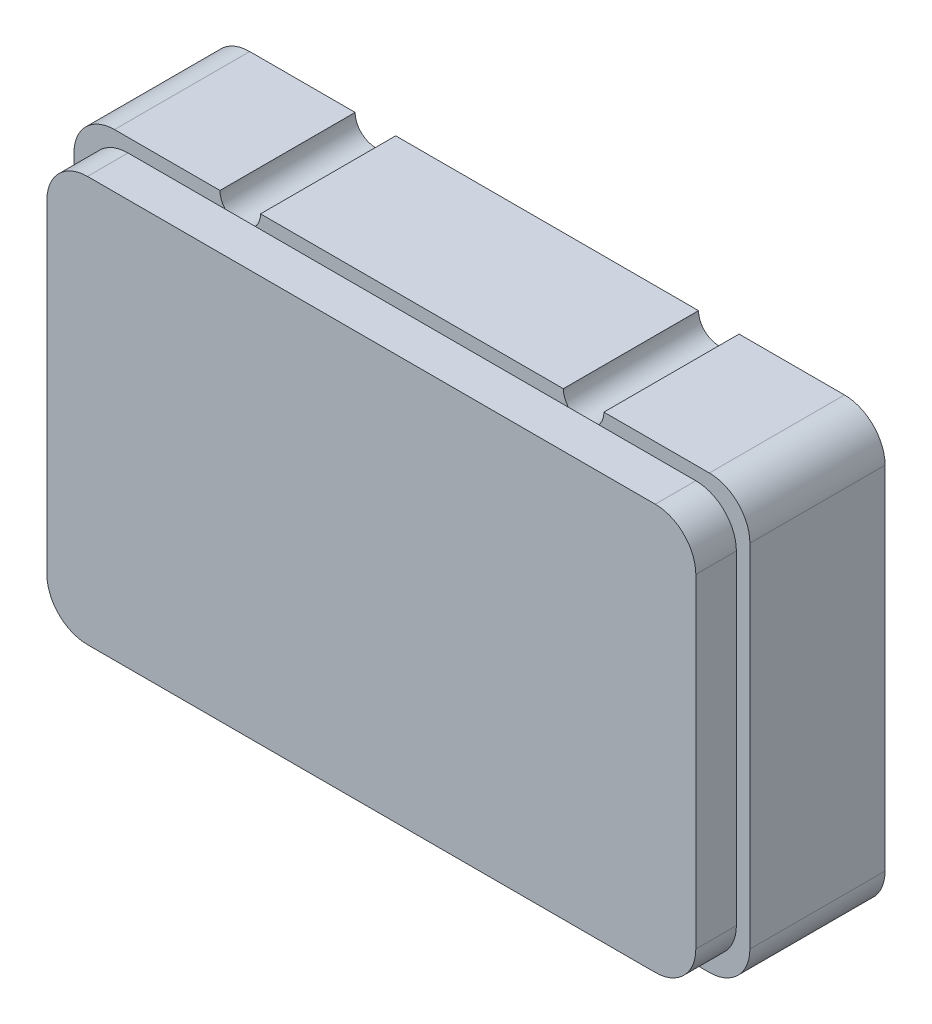
SolidWorks part; units mm, degrees
ref_plane "Front Plane" through (0, 0, 0) normal (0, 0, 1) x (1, 0, 0)
ref_plane "Top Plane" through (0, 0, 0) normal (0, 1, 0) x (1, 0, 0)
ref_plane "Right Plane" through (0, 0, 0) normal (1, 0, 0) x (0, 0, -1)
sketch "Sketch1" plane through (0, 0, 0) normal (0, 0, 1) x (1, 0, 0)
  line L1 (0, 0) -> (5, 0)
  line L2 (0, 0) -> (0, 3.2)
  line L3 (0, 3.2) -> (5, 3.2)
  line L4 (5, 0) -> (5, 3.2)
  dimension "D1" = 5
  dimension "D2" = 3.2
extrude "Boss-Extrude1" add sketch "Sketch1" along normal blind 1
sketch "Sketch2" plane through (0, 0, 1) normal (0, 0, 1) x (1, 0, 0)
  line L0 (2.5, 3.2) -> (2.5, 0) construction
  line L1 (0.1, 0.1) -> (4.9, 0.1)
  line L2 (0.1, 0.1) -> (0.1, 3.1)
  line L3 (0.1, 3.1) -> (4.9, 3.1)
  line L4 (4.9, 0.1) -> (4.9, 3.1)
  line L5 (5, 3.2) -> (0, 3.2) construction
  line L6 (0, 0) -> (5, 0) construction
  line L8 (0, 3.2) -> (0, 0) construction
  line L9 (0, 1.6) -> (5, 1.6) construction
  line L10 (5, 0) -> (5, 3.2) construction
  point P10 (2.5, 3.1)
  point P17 (0.1, 1.6)
  dimension "D1" = 4.8
  dimension "D2" = 3
extrude "Boss-Extrude2" add sketch "Sketch2" along normal blind 0.3
fillet "Fillet1" radius 0.3 4 edges at (4.9, 3.1, 1.15) (0.1, 3.1, 1.15) (0.1, 0.1, 1.15) (4.9, 0.1, 1.15)
fillet "Fillet2" radius 0.3 4 edges at (0, 3.2, 0.5) (0, 0, 0.5) (5, 0, 0.5) (5, 3.2, 0.5)
sketch "Sketch3" plane through (0, 0, 0) normal (0, 0, -1) x (-1, 0, 0)
  line L0 (-4.7, 3.2) -> (-0.3, 3.2) construction
  line L1 (-3.92, 3.2) -> (-3.62, 3.2)
  line L2 (-5, 0.3) -> (-5, 2.9) construction
  arc A0 (-3.92, 3.2) -> (-3.62, 3.2) centre (-3.77, 3.2) ccw
  dimension "D1" = 0.15
  dimension "D2" = 1.23
extrude "Cut-Extrude1" cut sketch "Sketch3" against normal up to surface (1 mm away) up to face at (2.5, 1.6, 1)
pattern_linear "LPattern1" count 2 spacing 2.54 along (-1, 0, 0) of "Cut-Extrude1"
ref_plane "Plane1" through (0, 1.6, 0) normal (0, 1, 0) x (1, 0, 0)
mirror "Mirror1" about plane through (0, 1.6, 0) normal (0, 1, 0) of "LPattern1", "Cut-Extrude1"
